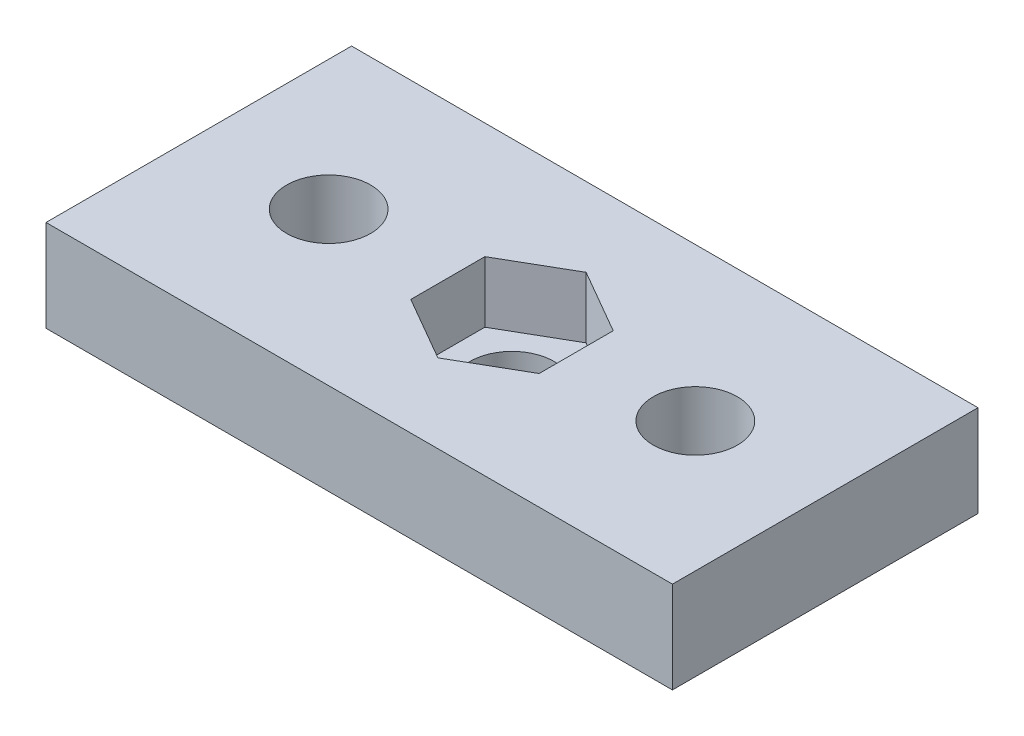
SolidWorks part; units mm, degrees
material "ABS"
ref_plane "Front Plane" through (0, 0, 0) normal (0, 0, 1) x (1, 0, 0)
ref_plane "Top Plane" through (0, 0, 0) normal (0, 1, 0) x (1, 0, 0)
ref_plane "Right Plane" through (0, 0, 0) normal (1, 0, 0) x (0, 0, -1)
sketch "Sketch1" plane through (0, 0, 0) normal (0, 1, 0) x (1, 0, 0)
  line L0 (0, 20) -> (0, 0)
  line L1 (0, 0) -> (41, 0)
  line L2 (41, 0) -> (41, 20)
  line L3 (41, 20) -> (0, 20)
  dimension "D1" = 41
  dimension "D2" = 20
extrude "Boss-Extrude1" add sketch "Sketch1" against normal blind 6
sketch "Sketch2" plane through (0, 0, 0) normal (0, 1, 0) x (1, 0, 0)
  line L6 (20.5, 20) -> (20.5, 0) construction
  line L7 (41, 20) -> (0, 20) construction
  line L8 (0, 0) -> (41, 0) construction
  line L9 (0, 10) -> (41, 10) construction
  line L10 (0, 20) -> (0, 0) construction
  line L11 (41, 0) -> (41, 20) construction
  line L13 (20.5, 5.1503) -> (24.7, 7.5751)
  line L14 (24.7, 7.5751) -> (24.7, 12.4249)
  line L15 (24.7, 12.4249) -> (20.5, 14.8497)
  line L16 (20.5, 14.8497) -> (16.3, 12.4249)
  line L17 (16.3, 12.4249) -> (16.3, 7.5751)
  line L18 (16.3, 7.5751) -> (20.5, 5.1503)
  circle A0 centre (20.5, 10) radius 4.2 construction
  dimension "D2" = 8.4
extrude "nut" cut sketch "Sketch2" against normal blind 4
sketch "Sketch7" plane through (0, 0, 0) normal (0, 1, 0) x (1, 0, 0)
  line L0 (20.5, 20) -> (20.5, 0) construction
  line L1 (41, 20) -> (0, 20) construction
  line L2 (0, 0) -> (41, 0) construction
  line L3 (0, 10) -> (41, 10) construction
  line L4 (0, 20) -> (0, 0) construction
  line L5 (41, 0) -> (41, 20) construction
  circle A0 centre (8.5, 10) radius 2.75
  circle A1 centre (32.5, 10) radius 2.75
  circle A2 centre (20.5, 10) radius 2.75
  dimension "D1" = 5.5
  dimension "D2" = 12
extrude "holes" cut sketch "Sketch7" against normal through all
